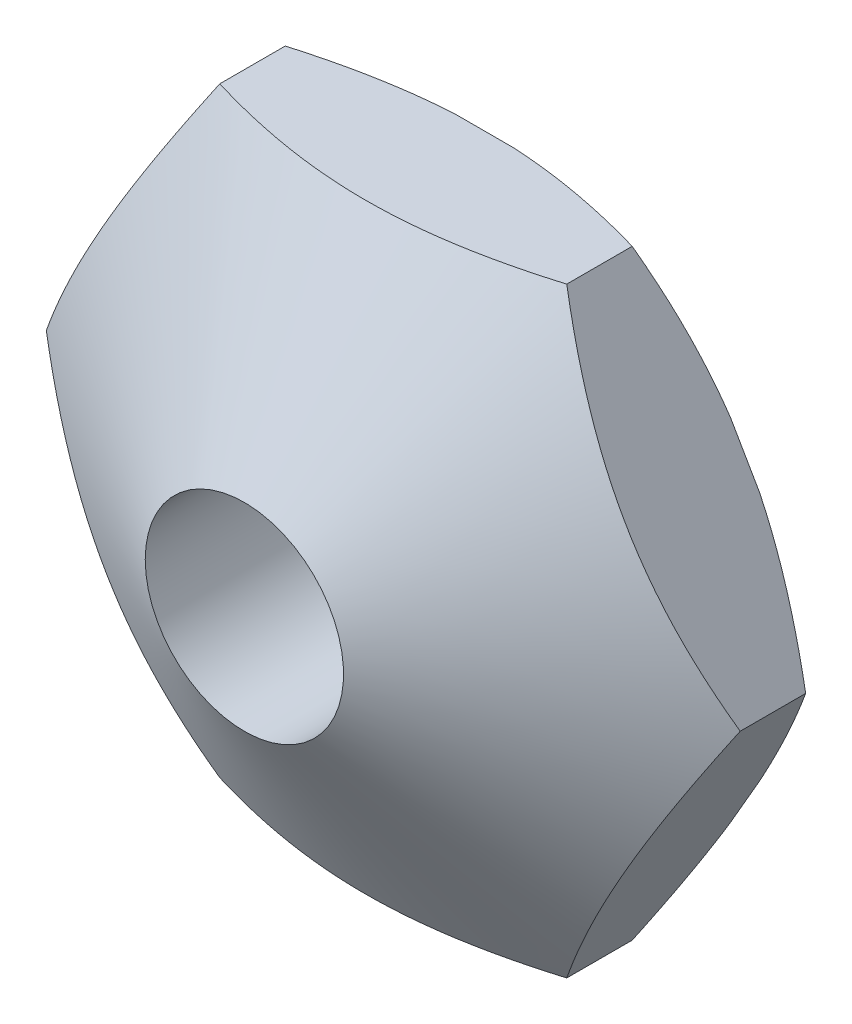
SolidWorks part; units mm, degrees
material "Brass"
ref_plane "Front Plane" through (0, 0, 0) normal (0, 0, 1) x (1, 0, 0)
ref_plane "Top Plane" through (0, 0, 0) normal (0, 1, 0) x (1, 0, 0)
ref_plane "Right Plane" through (0, 0, 0) normal (1, 0, 0) x (0, 0, -1)
sketch "Sketch1" plane through (0, 0, 0) normal (0, 0, 1) x (1, 0, 0)
  line L1 (-2.8868, 5) -> (-5.7735, 0)
  line L2 (-5.7735, 0) -> (-2.8868, -5)
  line L3 (-2.8868, -5) -> (2.8868, -5)
  line L4 (2.8868, -5) -> (5.7735, 0)
  line L5 (5.7735, 0) -> (2.8868, 5)
  line L6 (2.8868, 5) -> (-2.8868, 5)
  circle A0 centre (0, 0) radius 5 construction
  dimension "D1" = 10
extrude "Boss-Extrude1" add sketch "Sketch1" along normal blind 4
hole_wizard "M4x0.7 Tapped Hole1" positions "3DSketch1" profile "Sketch2" tap size "M4x0.7" standard "BSI" end condition through all
sketch3d "3DSketch1"
  point P0 (0, 0, 0)
  point P3 (0, 0, 0)
  point P6 (0, 0, 0)
sketch "Sketch2" plane through (0, 0, 0) normal (1, 0, 0) x (0, 1, 0)
  line L0 (0, 0) -> (0, 4)
  line L1 (0, 4) -> (1.65, 4)
  line L2 (1.65, 4) -> (1.65, 0)
  line L5 (1.65, 0) -> (0, 0)
  line L11 (0, -6.35) -> (0, 107.95) construction
  dimension "Thru Tap Drill Dia." = 3.3
  dimension "Thru Tap Drill Depth" = 4
cosmetic thread "Hole Thread1" parameters "D2"=4
cosmetic thread "Hole Thread2" parameters "D2"=4
cosmetic thread "Hole Thread3" parameters "D2"=4
ref_plane "Plane1" through (0, 0, 0) normal (0, 1, 0) x (1, 0, 0)
sketch "Sketch3" plane through (0, 0, 0) normal (0, 1, 0) x (1, 0, 0)
  line L0 (0, 0) -> (0, -4)
  line L1 (2.8868, 0) -> (-2.8868, 0) construction
  line L2 (2.8868, -4) -> (-2.8868, -4) construction
  line L3 (0, -4) -> (0, -9.4189)
  line L4 (1.65, -4) -> (6.0573, -1.3518)
  line L5 (6.0573, -0.3819) -> (6.0573, -4)
  line L7 (0, -4) -> (0, -8.6805)
  line L8 (1.65, -4) -> (6.0573, -4)
  line L9 (6.0573, -5.1261) -> (6.0573, -4)
  dimension "D1" = 1.65
  dimension "D2" = 59
revolve "Cut-Revolve3" cut sketch "Sketch3" angle 360 about L3
sketch "Sketch5" plane through (0, 0, 0) normal (0, 1, 0) x (1, 0, 0)
  line L0 (5.0235, 0) -> (5.7735, -0.433)
  line L1 (5.7735, 0) -> (2.8868, 0) construction
  line L2 (5.7735, -1.5223) -> (5.7735, 0) construction
  line L3 (5.7735, -0.433) -> (5.7735, 0)
  line L4 (5.7735, 0) -> (5.0235, 0)
  line L5 (0, 0) -> (0, -0.8992)
  dimension "D1" = 0.75
  dimension "D2" = 30
revolve "Cut-Revolve4" cut sketch "Sketch5" angle 360 about L5
